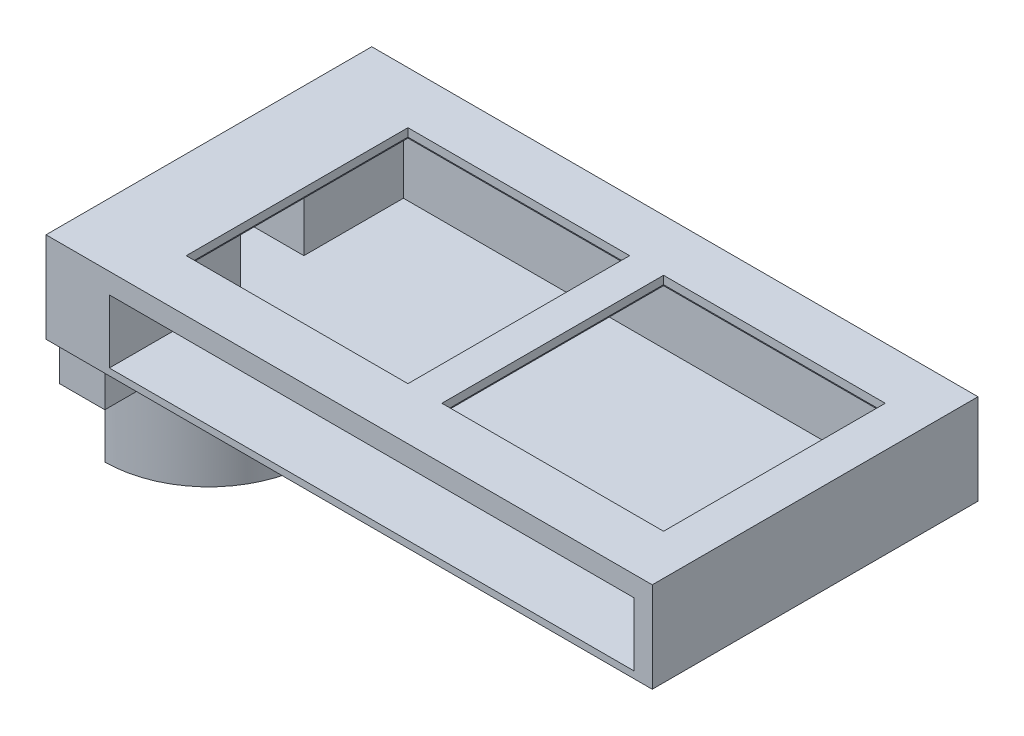
SolidWorks part; units mm, degrees
ref_plane "Front Plane" through (0, 0, 0) normal (0, 0, 1) x (1, 0, 0)
ref_plane "Top Plane" through (0, 0, 0) normal (0, 1, 0) x (1, 0, 0)
ref_plane "Right Plane" through (0, 0, 0) normal (1, 0, 0) x (0, 0, -1)
sketch "Sketch5" plane through (0, 0, 0) normal (0, 1, 0) x (1, 0, 0)
  line L0 (-124, 0) -> (-134, 0)
  line L1 (0, 0) -> (-1.9533, 0)
  line L2 (0, 0) -> (0, 72)
  line L3 (0, 72) -> (-134, 72)
  line L4 (-134, 0) -> (-134, 72)
  line L10 (-124, 0) -> (-1.9533, 0)
  dimension "D1" = 72
  dimension "D2" = 134
extrude "Main Body" add sketch "Sketch5" against normal blind 16
sketch "Sketch8" plane through (0, 0, 0) normal (0, 0, 1) x (1, 0, 0)
  line L0 (-134, -16) -> (-134, 0) construction
  line L1 (0, -16) -> (-134, -16)
  line L2 (0, -16) -> (0, -20)
  line L3 (0, -20) -> (-134, -20)
  line L4 (-134, -16) -> (-134, -20)
  dimension "D1" = 4
extrude "Cover" add sketch "Sketch8" against normal up to surface (72 mm away) up to face at (-67, -8, -72)
sketch "Sketch20" plane through (0, 0, 0) normal (0, 0, 1) x (1, 0, 0)
  line L0 (-134, -20) -> (-134, 0) construction
  line L1 (-4, -4.5) -> (-120, -4.5)
  line L2 (-4, -4.5) -> (-4, -18.5)
  line L3 (-4, -18.5) -> (-120, -18.5)
  line L4 (-120, -4.5) -> (-120, -18.5)
  line L6 (0, 0) -> (-134, 0) construction
  dimension "D1" = 14
  dimension "D2" = 116
  dimension "D3" = 14
  dimension "D4" = 4.5
extrude "Crystal Slot" cut sketch "Sketch20" against normal blind 65 contours L2 L1 L4 L3
sketch "Sketch9" plane through (-134, 0, 0) normal (-1, 0, 0) x (0, 0, 1)
  line L3 (-29, -4.5) -> (-43, -4.5)
  line L4 (-43, -18.5) -> (-43, -4.5)
  line L5 (-72, -20) -> (-72, 0) construction
  line L6 (-65, -4.5) -> (0, -4.5) construction
  line L7 (-29, -4.5) -> (-29, -18.5)
  line L8 (-29, -18.5) -> (-43, -18.5)
  dimension "D1" = 14
  dimension "D2" = 14
  dimension "D3" = 29
  dimension "D4" = 0
extrude "SiPM Window" cut sketch "Sketch9" against normal up to surface (14 mm away) up to face at (-120, -11.5, -32.5)
sketch "Sketch10" plane through (0, -20, 0) normal (0, -1, 0) x (1, 0, 0)
  line L0 (-134, -72) -> (-134, 0) construction
  line L4 (-134, -72) -> (-134, 0) construction
  line L5 (-134, -72) -> (0, -72) construction
  line L6 (-134, -16) -> (-134, -13)
  line L7 (-134, -56) -> (-134, -59)
  arc A0 (-134, -56) -> (-134, -16) centre (-134, -36) ccw
  arc A1 (-134, -59) -> (-134, -13) centre (-134, -36) ccw
  line M4 (-134, 0) -> (-134, -72)
  line M8 (-134, 0) -> (-134, -72)
  dimension "D2" = 20
  dimension "D1" = 36
  dimension "D3" = 3
  dimension "D4" = 3
extrude "Tube Adapter" add sketch "Sketch10" along normal blind 30 contours A1 A0 M4 M8
sketch "Sketch11" plane through (0, -20, 0) normal (0, -1, 0) x (1, 0, 0)
  line L0 (-134, -59) -> (-134, -69)
  line L5 (-134, -72) -> (-134, -59) construction
  line L6 (-134, -69) -> (-124, -69)
  line L7 (-124, -69) -> (-124, -56.7123)
  arc A0 (-134, -59) -> (-124, -56.7123) centre (-134, -36) ccw
  dimension "D1" = 10
  dimension "D2" = 10
extrude "Right Screw Terminal" add sketch "Sketch11" along normal blind 10
sketch "Sketch12" plane through (-134, 0, 0) normal (-1, 0, 0) x (0, 0, 1)
  line L2 (-69, -30) -> (-69, -20) construction
  line L3 (-59, -30) -> (-69, -30) construction
  circle A0 centre (-64, -25) radius 1.524
  dimension "D3" = 5
  dimension "D1" = 3.048
  dimension "D2" = 5
extrude "Right Screw Hole" cut sketch "Sketch12" against normal up to next
sketch "Sketch13" plane through (0, -20, 0) normal (0, -1, 0) x (-1, 0, 0)
  line L2 (134, 13) -> (134, 3)
  line L3 (134, 3) -> (124, 3)
  line L4 (124, 15.2877) -> (124, 3)
  arc A0 (134, 13) -> (124, 15.2877) centre (134, 36) cw
  dimension "D1" = 10
  dimension "D2" = 10
extrude "Left Screw Terminal" add sketch "Sketch13" along normal blind 10
sketch "Sketch14" plane through (-134, 0, 0) normal (-1, 0, 0) x (0, 0, 1)
  line L0 (-3, -30) -> (-3, -20) construction
  line L1 (-3, -30) -> (-13, -30) construction
  circle A0 centre (-8, -25) radius 1.524
  dimension "D3" = 3.048
  dimension "D1" = 5
  dimension "D2" = 5
extrude "Left Screw Hole" cut sketch "Sketch14" against normal up to next
ref_plane "Plane1" through (-144, 0, 0) normal (-1, 0, 0) x (0, 0, 1)
sketch "Sketch18" plane through (-144, 0, 0) normal (-1, 0, 0) x (0, 0, 1)
  line L0 (-56, -50) -> (-56, -20) construction
  line L5 (-56, -50) -> (-16, -50) construction
  circle A0 centre (-36, -42.5) radius 1.524
  dimension "D1" = 3.048
  dimension "D2" = 20
  dimension "D3" = 7.5
extrude "Adapter Hole" cut sketch "Sketch18" against normal up to surface (32.9495 mm away)
sketch "Sketch21" plane through (0, -4.5, 0) normal (0, -1, 0) x (1, 0, 0)
  line L0 (-4, -65) -> (-4, 0) construction
  line L1 (-6.5, -9) -> (-60.5, -9)
  line L2 (-6.5, -9) -> (-6.5, -63)
  line L3 (-6.5, -63) -> (-60.5, -63)
  line L4 (-60.5, -9) -> (-60.5, -63)
  line L5 (-63, -9) -> (-117, -9)
  line L6 (-63, -9) -> (-63, -63)
  line L7 (-63, -63) -> (-117, -63)
  line L8 (-117, -9) -> (-117, -63)
  line L9 (-60.5, -36) -> (-6.5, -36) construction
  line L10 (0, -36) -> (-117, -36) construction
  line L11 (0, -72) -> (0, 0) construction
  line L13 (-117, -36) -> (-63, -36) construction
  dimension "D1" = 2.5
  dimension "D2" = 54
  dimension "D3" = 54
  dimension "D4" = 54
  dimension "D5" = 2.5
  dimension "D6" = 54
extrude "Filter Slot" cut sketch "Sketch21" against normal blind 2.7
sketch "Sketch24" plane through (0, -1.8, 0) normal (0, -1, 0) x (1, 0, 0)
  line L0 (-117, -9) -> (-117, -63) construction
  line L1 (-9, -11.5) -> (-58, -11.5)
  line L2 (-9, -11.5) -> (-9, -60.5)
  line L3 (-9, -60.5) -> (-58, -60.5)
  line L4 (-58, -11.5) -> (-58, -60.5)
  line L5 (-6.5, -9) -> (-60.5, -9) construction
  line L7 (-117, -63) -> (-63, -63) construction
  line L9 (-6.5, -63) -> (-6.5, -9) construction
  line L10 (-60.5, -63) -> (-6.5, -63) construction
  line L11 (-60.5, -9) -> (-60.5, -63) construction
  line L12 (-63, -9) -> (-117, -9) construction
  line L13 (-114.5, -11.5) -> (-65.5, -11.5)
  line L14 (-114.5, -11.5) -> (-114.5, -60.5)
  line L15 (-114.5, -60.5) -> (-65.5, -60.5)
  line L16 (-65.5, -11.5) -> (-65.5, -60.5)
  line L17 (-63, -63) -> (-63, -9) construction
  dimension "D1" = 2.5
  dimension "D2" = 2.5
  dimension "D3" = 2.5
  dimension "D4" = 2.5
  dimension "D5" = 2.5
  dimension "D6" = 2.5
  dimension "D7" = 2.5
  dimension "D8" = 2.5
extrude "Filter Window" cut sketch "Sketch24" against normal up to surface (1.8 mm away) up to face at (-67, 0, -36)
